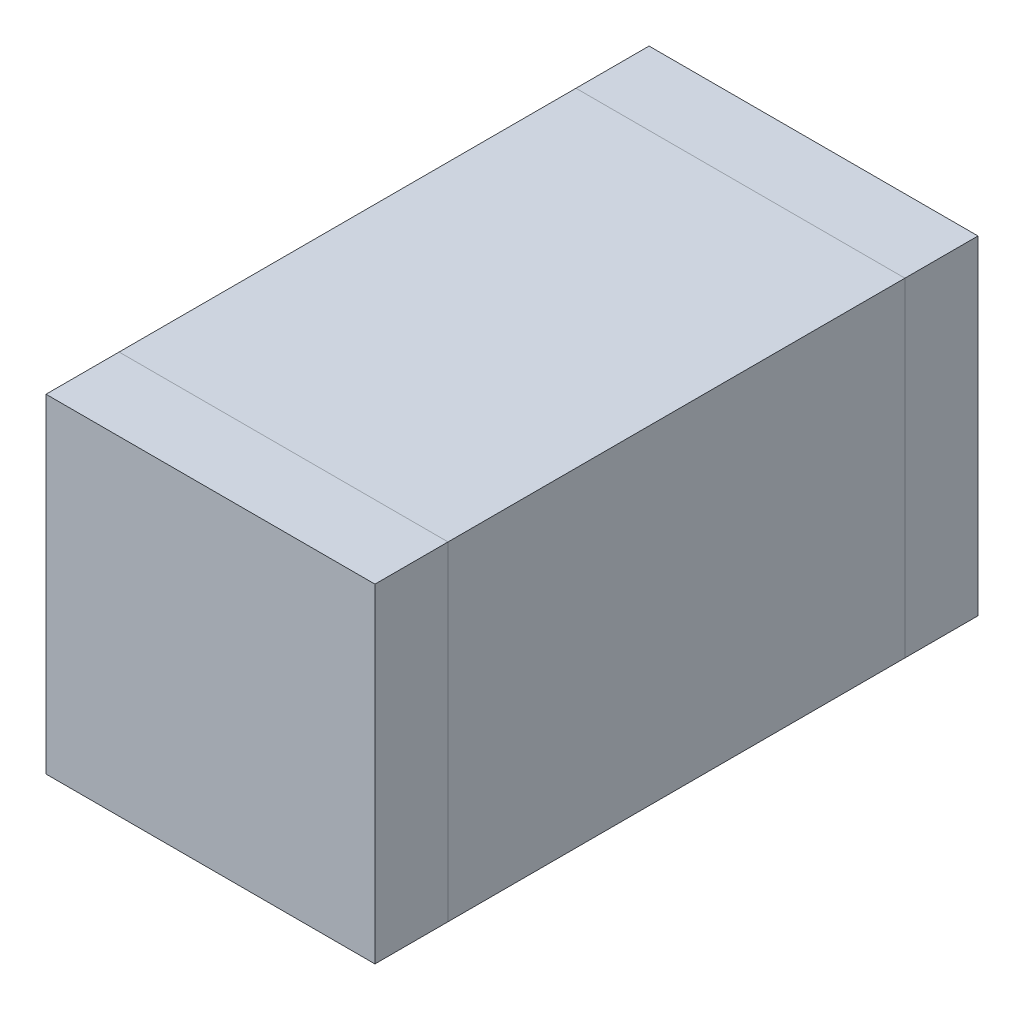
SolidWorks part; units mm, degrees
ref_plane "Front Plane" through (0, 0, 0) normal (0, 0, 1) x (1, 0, 0)
ref_plane "Top Plane" through (0, 0, 0) normal (0, 1, 0) x (1, 0, 0)
ref_plane "Right Plane" through (0, 0, 0) normal (1, 0, 0) x (0, 0, -1)
sketch "Sketch1" plane through (0, 0, 0) normal (0, 1, 0) x (1, 0, 0)
  line L1 (-0.9, 1.25) -> (0.9, 1.25)
  line L2 (-0.9, 1.25) -> (-0.9, -1.25)
  line L3 (-0.9, -1.25) -> (0.9, -1.25)
  line L4 (0.9, 1.25) -> (0.9, -1.25)
  line L5 (-0.9, 1.25) -> (0.9, -1.25) construction
  line L6 (-0.9, -1.25) -> (0.9, 1.25) construction
  point P0 (0, 0)
  dimension "Length" = 2.5
  dimension "Width" = 1.8
extrude "MB" add sketch "Sketch1" along normal blind 1.8
sketch "Sketch2" plane through (0, 0, 1.25) normal (0, 0, 1) x (1, 0, 0)
  line L4 (-0.9, 0) -> (0.9, 0)
  line L5 (0.9, 0) -> (0.9, 1.8)
  line L6 (0.9, 1.8) -> (-0.9, 1.8)
  line L7 (-0.9, 1.8) -> (-0.9, 0)
  line L8 (-0.9, 0) -> (0.9, 0)
  line L9 (0.9, 0) -> (0.9, 1.8)
  line L10 (0.9, 1.8) -> (-0.9, 1.8)
  line L11 (-0.9, 1.8) -> (-0.9, 0)
  dimension "D1" = 0
extrude "SB L" add sketch "Sketch2" along normal blind 0.4 separate body
sketch "Sketch3" plane through (0, 0, -1.25) normal (0, 0, -1) x (-1, 0, 0)
  line L4 (-0.9, 0) -> (0.9, 0)
  line L5 (0.9, 0) -> (0.9, 1.8)
  line L6 (0.9, 1.8) -> (-0.9, 1.8)
  line L7 (-0.9, 1.8) -> (-0.9, 0)
  line L8 (-0.9, 0) -> (0.9, 0)
  line L9 (0.9, 0) -> (0.9, 1.8)
  line L10 (0.9, 1.8) -> (-0.9, 1.8)
  line L11 (-0.9, 1.8) -> (-0.9, 0)
  dimension "D1" = 0
extrude "SB R" add sketch "Sketch3" along normal blind 0.4 separate body
